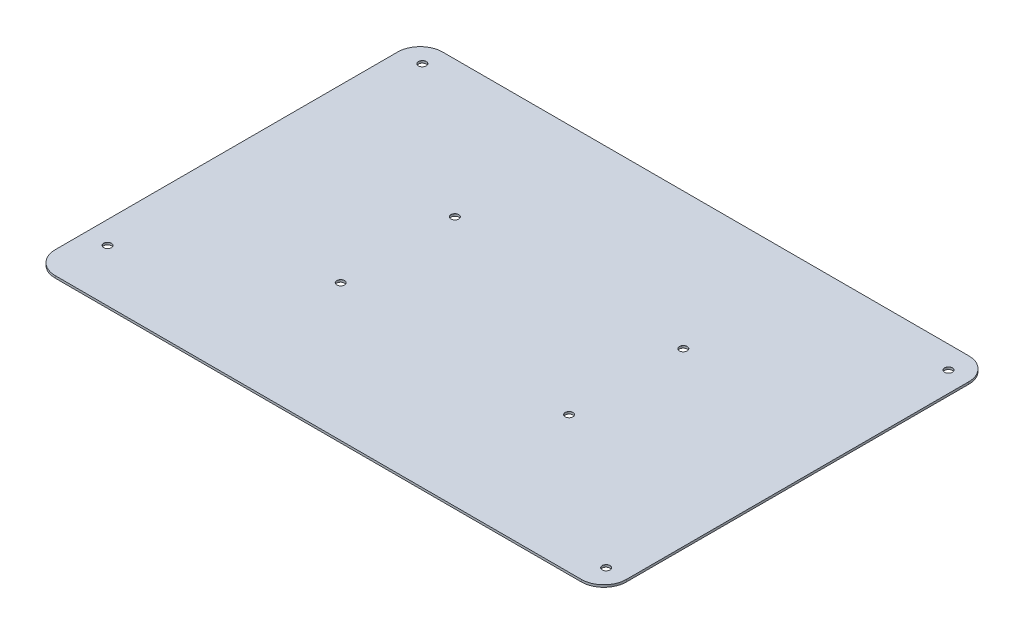
SolidWorks part; units mm, degrees
ref_plane "Front Plane" through (0, 0, 0) normal (0, 0, 1) x (1, 0, 0)
ref_plane "Top Plane" through (0, 0, 0) normal (0, 1, 0) x (1, 0, 0)
ref_plane "Right Plane" through (0, 0, 0) normal (1, 0, 0) x (0, 0, -1)
sketch "Sketch1" plane through (0, 0, 0) normal (0, 1, 0) x (1, 0, 0)
  line L1 (-127, 86.135) -> (127, 86.135)
  line L2 (-127, 86.135) -> (-127, -86.135)
  line L3 (-127, -86.135) -> (127, -86.135)
  line L4 (127, 86.135) -> (127, -86.135)
  line L5 (-127, 86.135) -> (127, -86.135) construction
  line L6 (-127, -86.135) -> (127, 86.135) construction
  point P0 (0, 0)
  dimension "D1" = 254
  dimension "D2" = 172.27
extrude "Boss-Extrude1" add sketch "Sketch1" along normal blind 1
fillet "Fillet1" radius 10 4 edges at (-127, 0.5, 86.135) (127, 0.5, 86.135) (127, 0.5, -86.135) (-127, 0.5, -86.135)
hole_wizard "M3 Clearance Hole1" positions "Sketch2" profile "Sketch3" hole size "M3" standard "ANSI Metric"
sketch "Sketch2" plane through (0, 1, 0) normal (0, 1, 0) x (1, 0, 0)
  line L1 (-50.8, 25.4) -> (50.8, 25.4)
  line L2 (-50.8, 25.4) -> (-50.8, -25.4)
  line L3 (-50.8, -25.4) -> (50.8, -25.4)
  line L4 (50.8, 25.4) -> (50.8, -25.4)
  line L5 (-50.8, 25.4) -> (50.8, -25.4) construction
  line L6 (-50.8, -25.4) -> (50.8, 25.4) construction
  line L7 (117, 86.135) -> (-117, 86.135) construction
  line L8 (-127, 76.135) -> (-127, -76.135) construction
  line L9 (-117, -86.135) -> (117, -86.135) construction
  line L10 (127, -76.135) -> (127, 76.135) construction
  point P0 (-117, 77.135)
  point P2 (-117, -62.865)
  point P4 (118, -76.135)
  point P6 (118, 76.135)
  point P8 (-50.8, -25.4)
  point P10 (50.8, -25.4)
  point P13 (-50.8, 25.4)
  point P15 (50.8, 25.4)
  point P19 (0, 0)
  dimension "D1" = 101.6
  dimension "D2" = 50.8
  dimension "D3" = 9
  dimension "D4" = 10
  dimension "D5" = 10
  dimension "D6" = 23.27
  dimension "D7" = 10
  dimension "D8" = 9
  dimension "D9" = 9
  dimension "D10" = 10
sketch "Sketch3" plane through (-117, 1, -77.135) normal (1, 0, 0) x (0, 0, 1)
  line L0 (0, 0) -> (0, 1)
  line L1 (0, 1) -> (1.7, 1)
  line L2 (1.7, 1) -> (1.7, 0.025)
  line L3 (1.7, 0.025) -> (1.725, 0)
  line L5 (1.725, 0) -> (0, 0)
  line L6 (-1.7, 0.025) -> (-1.725, 0) construction
  line L11 (0, -6.35) -> (0, 107.95) construction
  dimension "Thru Hole Dia." = 3.4
  dimension "Thru Hole Depth" = 1
  dimension "Near C'Sink Dia." = 3.45
  dimension "Near C'Sink Angle" = 90
